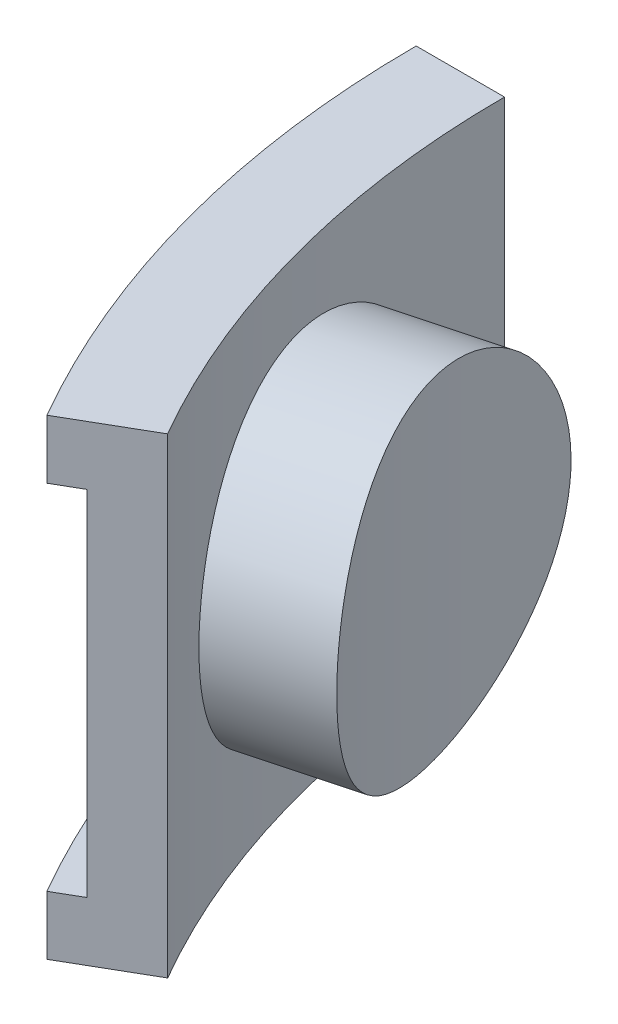
SolidWorks part; units mm, degrees
ref_plane "Front Plane" through (0, 0, 0) normal (0, 0, 1) x (1, 0, 0)
ref_plane "Top Plane" through (0, 0, 0) normal (0, 1, 0) x (1, 0, 0)
ref_plane "Right Plane" through (0, 0, 0) normal (1, 0, 0) x (0, 0, -1)
sketch "Sketch1" plane through (0, 0, 0) normal (0, 0, 1) x (1, 0, 0)
  line L0 (-43.4975, 0) -> (-43.4975, 2.54)
  line L1 (-43.4975, 2.54) -> (-42.2275, 2.54)
  line L2 (-42.2275, 2.54) -> (-42.2275, 17.78)
  line L3 (-42.2275, 17.78) -> (-43.4975, 17.78)
  line L4 (-43.4975, 17.78) -> (-43.4975, 20.32)
  line L5 (-43.4975, 20.32) -> (-39.6875, 20.32)
  line L6 (-39.6875, 20.32) -> (-39.6875, 0)
  line L7 (-39.6875, 0) -> (-43.4975, 0)
  line L8 (0, 0) -> (0, 20.32) construction
  dimension "D1" = 20.32
  dimension "D2" = 39.6875
  dimension "D3" = 15.24
  dimension "D4" = 3.81
  dimension "D5" = 2.54
revolve "Revolve1" add sketch "Sketch1" angle 30 about L8
ref_plane "Plane1" through (-37.0289, 0, 9.9219) normal (-0.9659, 0, 0.2588) x (0.2588, 0, 0.9659)
sketch "Sketch2" plane through (-37.0289, 0, 9.9219) normal (-0.9659, 0, 0.2588) x (0.2588, 0, 0.9659)
  line L0 (0, 0) -> (0, 10.16) construction
  circle A0 centre (0, 10.16) radius 7.1438
  dimension "D2" = 14.2875
  dimension "D1" = 10.16
extrude "Boss-Extrude1" add sketch "Sketch2" along normal blind 2.54
sketch "Sketch3" plane through (-37.0289, 0, 9.9219) normal (0.9659, 0, -0.2588) x (-0.2588, 0, -0.9659)
  circle A0 centre (0, 10.16) radius 7.1438
  circle A1 centre (0, 10.16) radius 7.1438 construction
extrude "Boss-Extrude2" add sketch "Sketch3" along normal blind 6.35
sketch "Sketch4" plane through (0, 0, 0) normal (0, 0, 1) x (1, 0, 0)
  line L1 (0, 0) -> (-34.925, 0)
  line L2 (0, 0) -> (0, 20.32)
  line L3 (0, 20.32) -> (-34.925, 20.32)
  line L4 (-34.925, 0) -> (-34.925, 20.32)
  dimension "D1" = 34.925
  dimension "D2" = 20.32
revolve "Cut-Revolve1" cut sketch "Sketch4" angle 30 about L2
